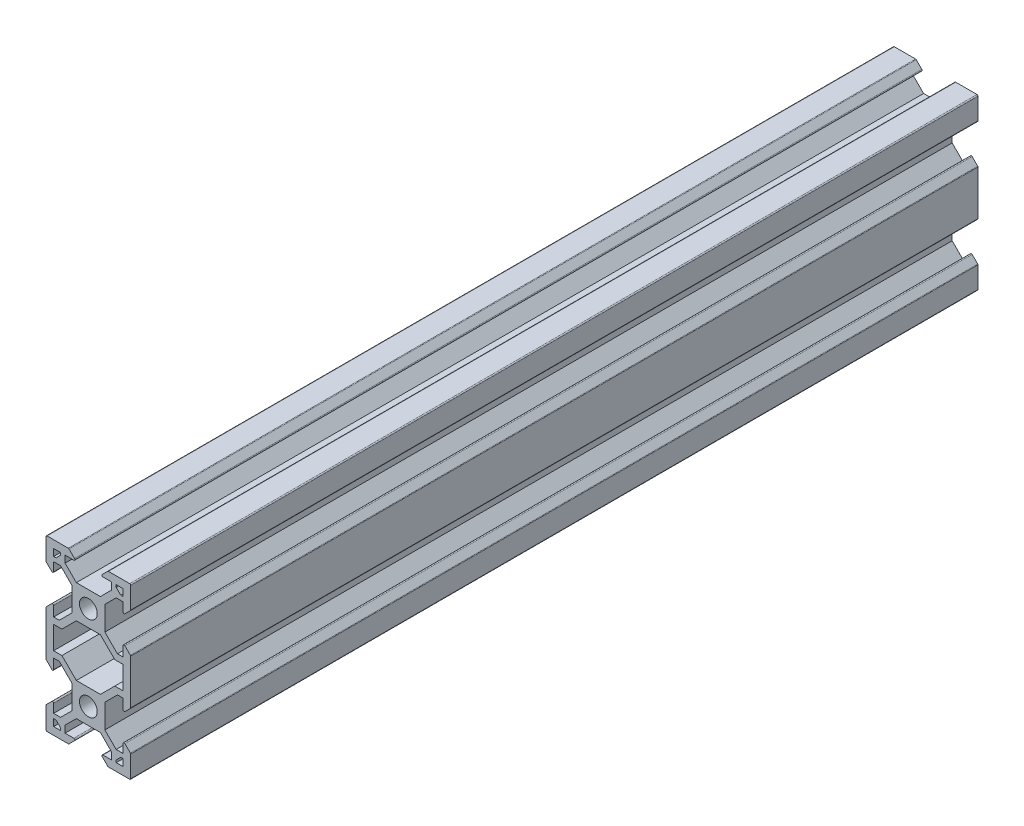
SolidWorks part; units mm, degrees
material "1060 Alloy"
ref_plane "Front Plane" through (0, 0, 0) normal (0, 0, 1) x (1, 0, 0)
ref_plane "Top Plane" through (0, 0, 0) normal (0, 1, 0) x (1, 0, 0)
ref_plane "Right Plane" through (0, 0, 0) normal (1, 0, 0) x (0, 0, -1)
sketch "Sketch1" plane through (0, 0, 0) normal (0, 0, 1) x (1, 0, 0)
  line L0 (8.2, -10) -> (10, -10)
  line L2 (10, -10) -> (10, -4.64)
  line L3 (10, -4.64) -> (8.2, -2.84)
  line L4 (8.2, -2.84) -> (8.2, -5.8007)
  line L5 (8.2, -5.8007) -> (6.8613, -5.8007)
  line L6 (6.8613, -5.8007) -> (3.9007, -2.84)
  line L7 (3.9007, -2.84) -> (3.9007, 2.84)
  line L8 (3.9007, 2.84) -> (6.56, 5.4993)
  line L9 (6.56, 5.4993) -> (8.2, 5.4993)
  line L10 (8.2, 5.4993) -> (8.2, 2.84)
  line L11 (8.2, 2.84) -> (10, 4.64)
  line L12 (10, 4.64) -> (10, 10)
  line L13 (10, 10) -> (4.64, 10)
  line L14 (4.64, 10) -> (2.84, 8.2)
  line L15 (2.84, 8.2) -> (5.4993, 8.2)
  line L16 (5.4993, 8.2) -> (5.4993, 6.56)
  line L17 (5.4993, 6.56) -> (2.84, 3.9007)
  line L18 (2.84, 3.9007) -> (-2.84, 3.9007)
  line L19 (-2.84, 3.9007) -> (-5.4993, 6.56)
  line L20 (-5.4993, 6.56) -> (-5.4993, 8.2)
  line L21 (-5.4993, 8.2) -> (-2.84, 8.2)
  line L22 (-2.84, 8.2) -> (-4.64, 10)
  line L23 (-4.64, 10) -> (-10, 10)
  line L24 (-10, 10) -> (-10, 4.64)
  line L25 (-10, 4.64) -> (-8.2, 2.84)
  line L26 (-8.2, 2.84) -> (-8.2, 5.4993)
  line L27 (-8.2, 5.4993) -> (-6.56, 5.4993)
  line L28 (-6.56, 5.4993) -> (-3.9007, 2.84)
  line L29 (-3.9007, 2.84) -> (-3.9007, -2.84)
  line L30 (-3.9007, -2.84) -> (-6.8613, -5.8007)
  line L31 (-6.8613, -5.8007) -> (-8.2, -5.8007)
  line L32 (-8.2, -5.8007) -> (-8.2, -2.84)
  line L33 (-8.2, -2.84) -> (-10, -4.64)
  line L34 (-10, -4.64) -> (-10, -10)
  line L64 (8.2, -7.3007) -> (8.2, -10)
  line L70 (-8.2, -10) -> (-8.2, -7.3007)
  line L71 (-8.2, -7.3007) -> (-6.24, -7.3007)
  line L72 (-6.24, -7.3007) -> (-2.84, -3.9007)
  line L73 (-2.84, -3.9007) -> (2.84, -3.9007)
  line L74 (2.84, -3.9007) -> (6.24, -7.3007)
  line L75 (6.24, -7.3007) -> (8.2, -7.3007)
  line L76 (-10, -10) -> (-8.2, -10)
  circle A0 centre (0, 0) radius 2.1
  point P46 (0, -3.9007)
  point P47 (0, 3.9007)
  point P49 (-3.9007, 0)
  point P50 (3.9007, 0)
  dimension "D1" = 4.2
  dimension "D8" = 1.8
  dimension "D2" = 20
  dimension "D3" = 20
  dimension "D4" = 5.68
  dimension "D5" = 90
  dimension "D6" = 10
  dimension "D7" = 10
  dimension "D9" = 1.8
  dimension "D10" = 1.8
  dimension "D11" = 1.5
  dimension "D12" = 1.5
  dimension "D13" = 1.64
  dimension "D14" = 1.5
  dimension "D15" = 1.96
extrude "Boss-Extrude2" add sketch "Sketch1" along normal blind 200
sketch "Sketch2" plane through (0, 0, 200) normal (0, 0, 1) x (1, 0, 0)
  line L0 (-8.2, 2.84) -> (-8.2, 5.4993) construction
  line L1 (-5.4993, 8.2) -> (-2.84, 8.2) construction
  line L2 (-8.2, 6.5693) -> (-8.2, 8.2)
  line L3 (-8.2, 8.2) -> (-6.5693, 8.2)
  line L4 (8.2, 5.4993) -> (8.2, 2.84) construction
  line L5 (8.2, 8.2) -> (8.2, 6.5693)
  line L6 (3.9007, 2.84) -> (6.56, 5.4993) construction
  line L7 (-5.4993, 6.56) -> (-5.4993, 8.2) construction
  line L8 (6.56, 5.4993) -> (8.2, 5.4993) construction
  line L11 (6.5693, 8.2) -> (6.5693, 6.56)
  line L12 (6.5693, 8.2) -> (6.5693, 7.63)
  line L16 (6.5693, 8.2) -> (8.2, 8.2)
  line L17 (-8.2, 6.5693) -> (-6.56, 6.5693)
  line L18 (-8.2, 6.5693) -> (-7.63, 6.5693)
  line L19 (-7.63, 6.5693) -> (-6.5693, 7.63)
  line L20 (6.5693, 7.63) -> (7.63, 6.5693)
  line L22 (7.63, 6.5693) -> (8.2, 6.5693)
  line L24 (-6.5693, 7.63) -> (-6.5693, 8.2)
  dimension "D5" = 1.5
  dimension "D1" = 1.07
  dimension "D3" = 1.07
  dimension "D2" = 1.07
  dimension "D4" = 1.07
extrude "Cut-Extrude1" cut sketch "Sketch2" against normal through all
fillet "Fillet1" radius 0.25 14 edges at (8.2, 2.84, 100) (-10, 4.64, 100) (-4.64, 10, 100) (4.64, 10, 100) (-10, -4.64, 100) (-10, 10, 100) (10, -4.64, 100) (10, 10, 100) (8.2, -2.84, 100) (-8.2, -2.84, 100) (-8.2, 2.84, 100) (10, 4.64, 100) (2.84, 8.2, 100) (-2.84, 8.2, 100)
ref_plane "Plane1" through (0, -10, 0) normal (0, -1, 0) x (-1, 0, 0)
mirror "Mirror1" about plane through (0, -10, 0) normal (0, -1, 0) of "Fillet1", "Boss-Extrude2"
mirror "Mirror2" about plane through (0, -10, 0) normal (0, -1, 0) of "Cut-Extrude1"
